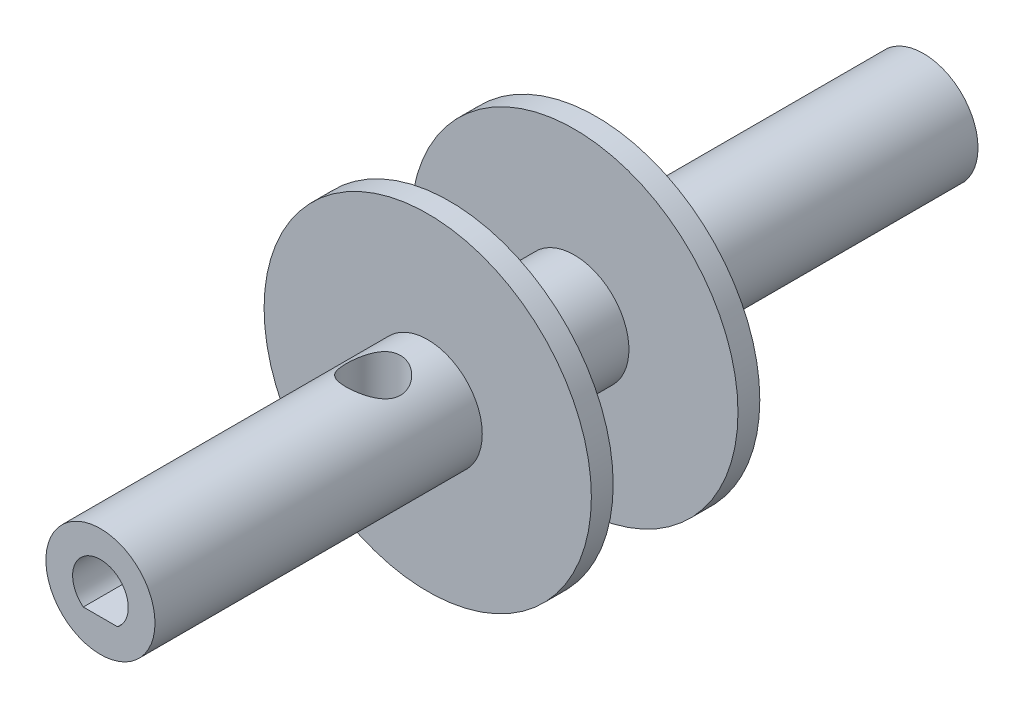
SolidWorks part; units mm, degrees
ref_plane "Front Plane" through (0, 0, 0) normal (0, 0, 1) x (1, 0, 0)
ref_plane "Top Plane" through (0, 0, 0) normal (0, 1, 0) x (1, 0, 0)
ref_plane "Right Plane" through (0, 0, 0) normal (1, 0, 0) x (0, 0, -1)
sketch "Sketch1" plane through (0, 0, 0) normal (0, 0, 1) x (1, 0, 0)
  circle A0 centre (0, 0) radius 6.35
extrude "Boss-Extrude1" add sketch "Sketch1" along normal blind 95.8088
sketch "Sketch2" plane through (0, 0, 95.8088) normal (0, 0, 1) x (1, 0, 0)
  line L0 (0, 3.2385) -> (0, -2.5527) construction
  line L1 (-1.9929, -2.5527) -> (1.9929, -2.5527)
  arc A0 (1.9929, -2.5527) -> (-1.9929, -2.5527) centre (0, 0) ccw
  arc A1 (1.9929, -2.5527) -> (-1.9929, -2.5527) centre (0, 0) ccw
  dimension "D1" = 6.477
  dimension "D2" = 5.7912
sketch "Sketch4" plane through (0, 0, 0) normal (0, 1, 0) x (1, 0, 0)
  line L0 (0, -95.8088) -> (0, -83.1088)
  line L1 (-6.35, -95.8088) -> (6.35, -95.8088) construction
  line L2 (0, 0) -> (0, -12.7)
  line L3 (6.35, 0) -> (-6.35, 0) construction
  line L4 (0, -83.1088) -> (0, -64.0588) construction
  line L5 (0, -12.7) -> (0, -31.75)
  circle A0 centre (0, -83.1088) radius 3.175
  circle A1 centre (0, -12.7) radius 3.175
  circle A2 centre (0, -64.0588) radius 3.175
  circle A3 centre (0, -31.75) radius 3.175
  dimension "D1" = 6.35
  dimension "D2" = 6.35
  dimension "D4" = 19.05
  dimension "D3" = 12.7
  dimension "D5" = 19.05
  dimension "D6" = 12.7
extrude "Cut-Extrude2" cut sketch "Sketch4" against normal through all both and the other way through all contours A2 | A3
ref_plane "Plane1" through (0, 0, 57.7088) normal (0, 0, 1) x (1, 0, 0)
sketch "Sketch5" plane through (0, 0, 57.7088) normal (0, 0, 1) x (1, 0, 0)
  circle A0 centre (0, 0) radius 19.05
  dimension "D1" = 38.1
extrude "Boss-Extrude2" add sketch "Sketch5" against normal blind 2.54
ref_plane "Plane2" through (0, 0, 38.1) normal (0, 0, -1) x (-1, 0, 0)
sketch "Sketch6" plane through (0, 0, 38.1) normal (0, 0, -1) x (-1, 0, 0)
  circle A0 centre (0, 0) radius 19.05
  dimension "D1" = 38.1
extrude "Boss-Extrude3" add sketch "Sketch6" against normal blind 2.54
extrude "Cut-Extrude4" cut sketch "Sketch2" against normal blind 27.94 contours L0 A1 L1 | A0 L0 L1
sketch "Sketch7" plane through (0, 0, 0) normal (0, 0, -1) x (-1, 0, 0)
  line L0 (3.2385, 0) -> (-2.5527, 0) construction
  line L2 (-2.5527, -1.9929) -> (-2.5527, 1.9929)
  circle A0 centre (0, 0) radius 3.2385
  dimension "D1" = 6.477
  dimension "D3" = 5.7912
extrude "Cut-Extrude5" cut sketch "Sketch7" against normal blind 27.94 contours L0 A0 L2 | A0 L0 L2
